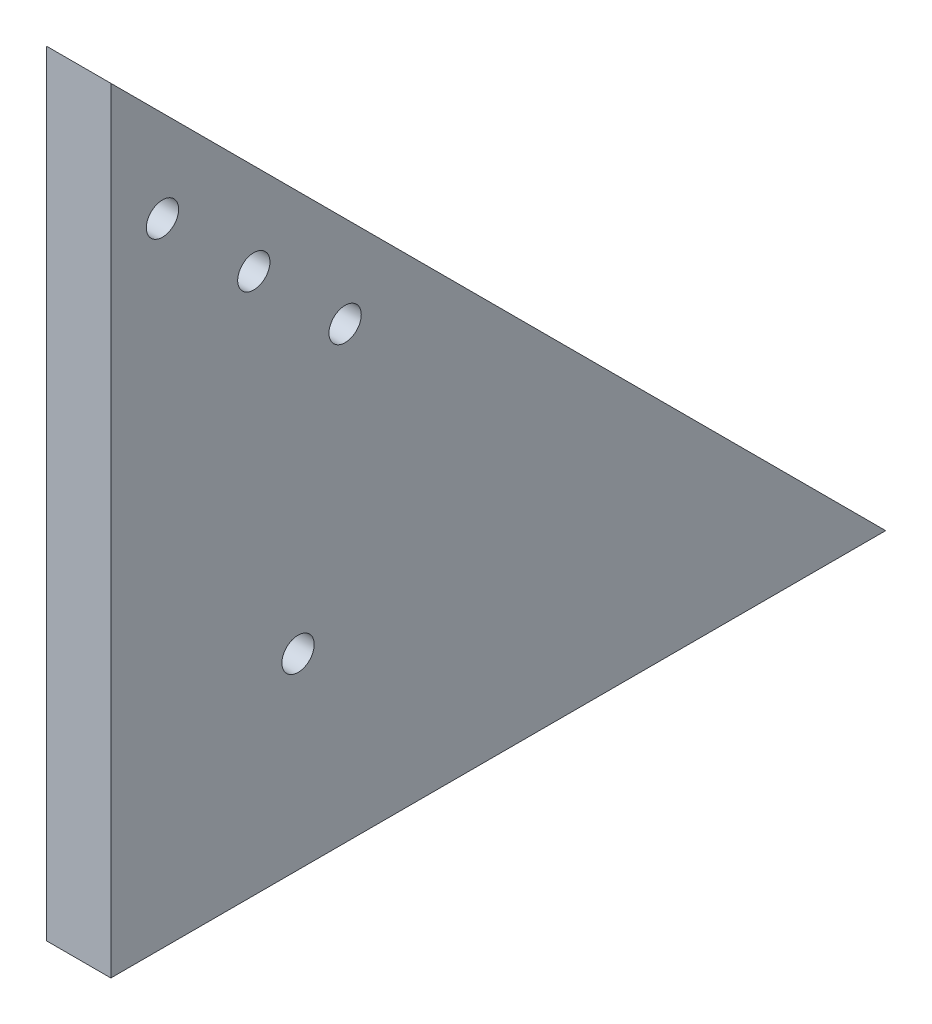
SolidWorks part; units mm, degrees
ref_plane "Front Plane" through (0, 0, 0) normal (0, 0, 1) x (1, 0, 0)
ref_plane "Top Plane" through (0, 0, 0) normal (0, 1, 0) x (1, 0, 0)
ref_plane "Right Plane" through (0, 0, 0) normal (1, 0, 0) x (0, 0, -1)
sketch "Sketch1" plane through (0, 0, 0) normal (1, 0, 0) x (0, 0, -1)
  line L0 (0, 0) -> (0, 120)
  line L2 (0, 0) -> (120, 0)
  line L4 (120, 0) -> (0, 120)
  dimension "D1" = 120
  dimension "D2" = 120
extrude "Boss-Extrude1" add sketch "Sketch1" along normal blind 10
sketch "Sketch4" plane through (10, 0, 0) normal (1, 0, 0) x (0, 0, -1)
  line L0 (0, 0) -> (31.0179, 31.0179) construction
  line L1 (120, 0) -> (0, 120) construction
  circle A0 centre (22.1372, 83.7206) radius 2.5
  circle A1 centre (36.2794, 69.5785) radius 2.5
  circle A2 centre (7.9951, 97.8628) radius 2.5
  circle A3 centre (28.9914, 28.9914) radius 2.5
  dimension "D1" = 20
  dimension "D6" = 41
  dimension "D2" = 20
  dimension "D3" = 10
  dimension "D4" = 10
  dimension "D5" = 10
  dimension "D7" = 42.5
extrude "Cut-Extrude3" cut sketch "Sketch4" against normal blind 10
